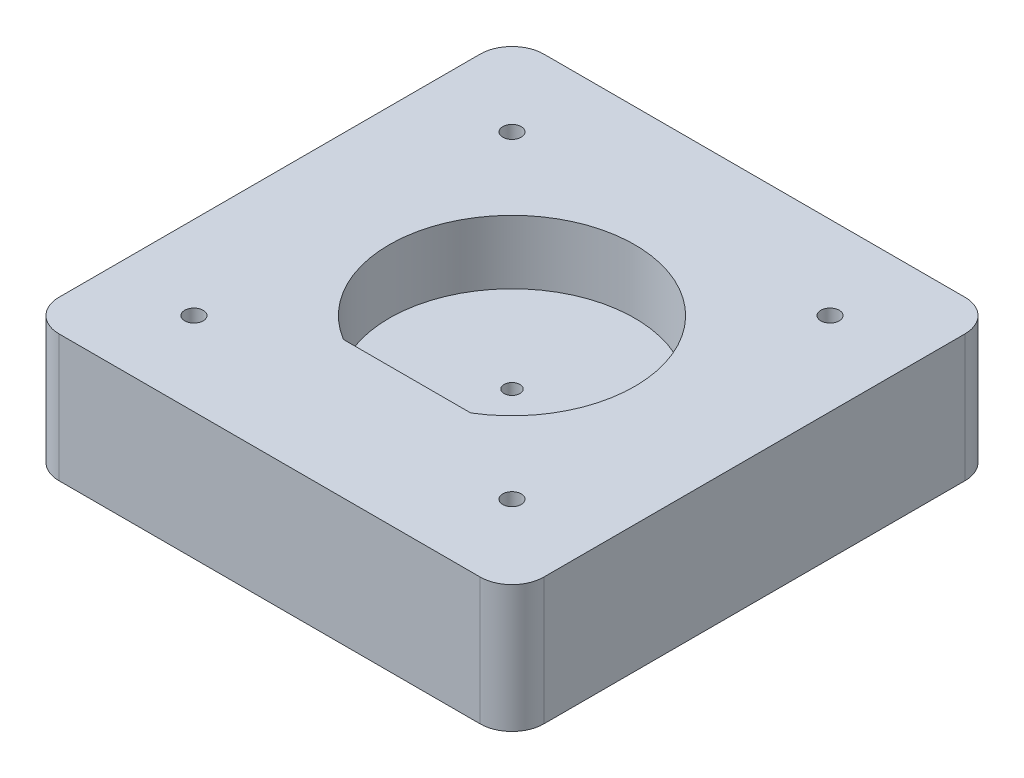
SolidWorks part; units mm, degrees
ref_plane "Front Plane" through (0, 0, 0) normal (0, 0, 1) x (1, 0, 0)
ref_plane "Top Plane" through (0, 0, 0) normal (0, 1, 0) x (1, 0, 0)
ref_plane "Right Plane" through (0, 0, 0) normal (1, 0, 0) x (0, 0, -1)
sketch "Sketch2" plane through (0, 0, 0) normal (0, 1, 0) x (1, 0, 0)
  line L0 (-38.1, -38.1) -> (38.1, -38.1)
  line L1 (-38.1, -38.1) -> (-38.1, 38.1)
  line L2 (-38.1, 38.1) -> (38.1, 38.1)
  line L3 (38.1, -38.1) -> (38.1, 38.1)
  line L4 (-38.1, -38.1) -> (38.1, 38.1) construction
  line L5 (-38.1, 38.1) -> (38.1, -38.1) construction
  point P0 (0, 0)
  dimension "D1" = 76.2
extrude "Boss-Extrude1" add sketch "Sketch2" along normal blind 20
sketch "Sketch3" plane through (0, 20, 0) normal (0, 1, 0) x (1, 0, 0)
  line L0 (-10, -16.5073) -> (10, -16.5073)
  arc A0 (10, -16.5073) -> (-10, -16.5073) centre (0, 0) ccw
  dimension "D1" = 38.6
  dimension "D2" = 20
extrude "Cut-Extrude1" cut sketch "Sketch3" against normal blind 10
sketch "Sketch4" plane through (0, 0, 0) normal (0, -1, 0) x (1, 0, 0)
  circle A0 centre (0, 0) radius 10
  dimension "D1" = 20
extrude "Cut-Extrude2" cut sketch "Sketch4" against normal blind 5
hole_wizard "Tap Drill for M3x0.5 Tap1" positions "Sketch5" profile "Sketch6" hole size "M3x0.5" standard "ANSI Metric" end condition through all
sketch "Sketch5" plane through (0, 5, 0) normal (0, -1, 0) x (-1, 0, 0)
  point P0 (0, 0)
sketch "Sketch6" plane through (0, 5, 0) normal (1, 0, 0) x (0, 0, -1)
  line L0 (0, 0) -> (0, 15)
  line L1 (0, 15) -> (1.25, 15)
  line L2 (1.25, 15) -> (1.25, 0)
  line L5 (1.25, 0) -> (0, 0)
  line L11 (0, -6.35) -> (0, 107.95) construction
  dimension "Thru Hole Dia." = 2.5
  dimension "Thru Hole Depth" = 15
fillet "Fillet1" radius 5 4 edges at (38.1, 10, -38.1) (-38.1, 10, -38.1) (-38.1, 10, 38.1) (38.1, 10, 38.1)
hole_wizard "Tap Drill for M3.5x0.6 Tap1" positions "Sketch10" profile "Sketch9" hole size "M3.5x0.6" standard "ANSI Metric" end condition through all
sketch "Sketch10" plane through (0, 0, 0) normal (0, -1, 0) x (-1, 0, 0)
  line L1 (-25, -25) -> (25, -25) construction
  line L2 (-25, -25) -> (-25, 25) construction
  line L3 (-25, 25) -> (25, 25) construction
  line L4 (25, -25) -> (25, 25) construction
  line L5 (-25, -25) -> (25, 25) construction
  line L6 (-25, 25) -> (25, -25) construction
  point P2 (25, 25)
  point P5 (-25, -25)
  point P6 (-25, 25)
  point P7 (25, -25)
  point P47 (0, 0)
  dimension "D1" = 50
sketch "Sketch9" plane through (-25, 0, -25) normal (1, 0, 0) x (0, 0, -1)
  line L0 (0, 0) -> (0, 20)
  line L1 (0, 20) -> (1.45, 20)
  line L2 (1.45, 20) -> (1.45, 0)
  line L5 (1.45, 0) -> (0, 0)
  line L11 (0, -6.35) -> (0, 107.95) construction
  dimension "Thru Hole Dia." = 2.9
  dimension "Thru Hole Depth" = 20
equation "\"shaftDia\" = 38.1"
equation "\"D1@Sketch3\"=\"shaftDia\"  + 0.5"
